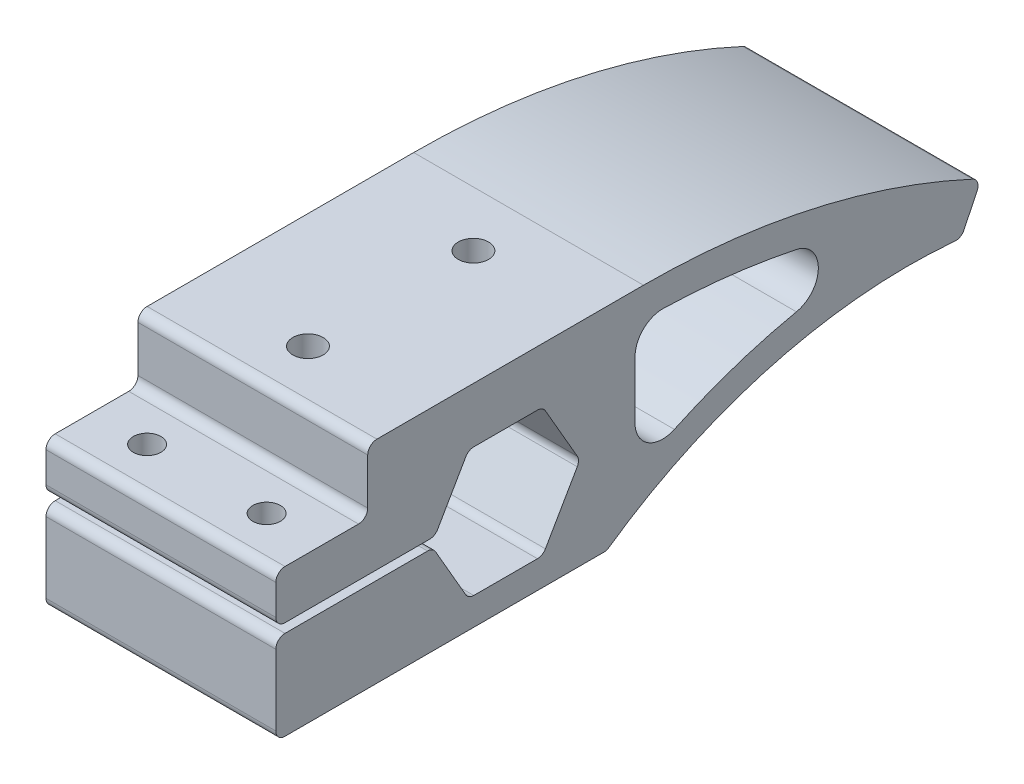
SolidWorks part; units mm, degrees
material "2014 Alloy"
ref_plane "Front Plane" through (0, 0, 0) normal (0, 0, 1) x (1, 0, 0)
ref_plane "Top Plane" through (0, 0, 0) normal (0, 1, 0) x (1, 0, 0)
ref_plane "Right Plane" through (0, 0, 0) normal (1, 0, 0) x (0, 0, -1)
sketch "Sketch1" plane through (0, 0, 0) normal (1, 0, 0) x (0, 0, -1)
  line L0 (0, 85) -> (-30, 85)
  line L1 (-30, 85) -> (-30, 78)
  line L2 (-30, 78) -> (-40, 78)
  line L3 (-40, 71.7) -> (-22.9097, 71.7)
  line L4 (-22.6788, 72.7) -> (-40, 72.7)
  line L5 (36.7289, 76.655) -> (34.5684, 72.1459)
  line L6 (-6.9171, 72) -> (-10.9585, 79)
  line L7 (-10.9585, 79) -> (-19.0415, 79)
  line L8 (-19.0415, 79) -> (-22.6788, 72.7)
  line L9 (-22.9097, 71.7) -> (-19.0415, 65)
  line L10 (-19.0415, 65) -> (-10.9585, 65)
  line L11 (-10.9585, 65) -> (-6.9171, 72)
  line L12 (-40, 72.7) -> (-40, 78)
  line L13 (-40, 71.7) -> (-40, 62)
  line L14 (-40, 62) -> (-4, 62)
  line L15 (-12.1097, 52.9939) -> (-16.8969, 61.2856) [skipped]
  line L17 (-0.9171, 72.4558) -> (-0.9171, 78.7311)
  circle A0 centre (0, 0) radius 85 construction
  arc A1 (0, 85) -> (36.7289, 76.655) centre (0, 0) cw
  circle A2 centre (-15, 72) radius 7 construction
  arc A3 (34.5684, 72.1459) -> (-4, 62) centre (28.8691, 15.4315) ccw
  arc A4 (-0.9171, 78.7311) -> (2.1631, 81.7301) centre (2.0829, 78.7311) cw
  arc A5 (-0.9171, 72.4558) -> (3.357, 69.7398) centre (2.0829, 72.4558) ccw
  arc A6 (2.1631, 81.7301) -> (16.6347, 80.0466) centre (-0.0247, -0.1191) cw
  arc A7 (3.357, 69.7398) -> (16.637, 74.1725) centre (28.938, 15.2109) cw
  arc A8 (16.6347, 80.0466) -> (16.637, 74.1725) centre (16.0243, 77.1093) cw
  dimension "D1" = 170
  dimension "D4" = 10
  dimension "D5" = 5
  dimension "D7" = 3
  dimension "D11" = 3
  dimension "D14" = 6
  dimension "D13" = 3
  dimension "D15" = 14
  dimension "D16" = 1
  dimension "D17" = 16
  dimension "D8" = 3
  dimension "D18" = 57
  dimension "D2" = 30
  dimension "D3" = 7
  dimension "D9" = 15
  dimension "D10" = 9.7
  dimension "D12" = 36
extrude "Boss-Extrude1" add sketch "Sketch1" along normal blind 25
fillet "Fillet1" radius 1 16 edges at (12.5, 85, 30) (12.5, 78, 30) (12.5, 78, 40) (12.5, 62, 40) (12.5, 76.655, -36.7289) (12.5, 65, 19.0415) (12.5, 71.7, 22.9097) (12.5, 72.7, 22.6788) (12.5, 79, 19.0415) (12.5, 79, 10.9585) (12.5, 72, 6.9171) (12.5, 65, 10.9585) (12.5, 72.7, 40) (12.5, 71.7, 40) (12.5, 62, 4) (12.5, 72.1459, -34.5684)
hole_wizard "Ø3.0mm Dowel Hole1" positions "Sketch3" profile "Sketch4" hole size "Ø3.0" standard "ISO" end condition through all
sketch "Sketch3" plane through (0, 78, 0) normal (0, 1, 0) x (1, 0, 0)
  line L0 (0, -31) -> (0, -39) construction
  line L1 (25, -31) -> (25, -39) construction
  line L2 (25, -40) -> (0, -40) construction
  point P0 (6, -35)
  point P2 (19, -35)
  dimension "D1" = 6
  dimension "D2" = 6
  dimension "D3" = 5
sketch "Sketch4" plane through (6, 78, 35) normal (1, 0, 0) x (0, 0, 1)
  line L0 (0, 0) -> (0, 16)
  line L1 (0, 16) -> (1.5, 16)
  line L2 (1.5, 16) -> (1.5, 0)
  line L5 (1.5, 0) -> (0, 0)
  line L11 (0, -6.35) -> (0, 107.95) construction
  dimension "Thru Hole Dia." = 3
  dimension "Thru Hole Depth" = 16
hole_wizard "M4 Tapped Hole1" positions "Sketch6" profile "Sketch7" tap size "M4" standard "ISO"
sketch "Sketch6" plane through (0, 85, 0) normal (0, 1, 0) x (1, 0, 0)
  line L0 (0, 0) -> (0, -29) construction
  line L1 (25, -30) -> (0, -30) construction
  point P10 (12.5, -24)
  point P17 (12.5, -6)
  dimension "D1" = 12.5
  dimension "D2" = 6
  dimension "D3" = 18
sketch "Sketch7" plane through (12.5, 85, 24) normal (1, 0, 0) x (0, 0, 1)
  line L0 (0, 0) -> (0, 11.0914)
  line L1 (0, 11.0914) -> (1.65, 10.1)
  line L2 (1.65, 10.1) -> (1.65, 0)
  line L5 (1.65, 0) -> (0, 0)
  line L10 (0, 11.0914) -> (-1.65, 10.1) construction
  line L11 (0, -6.35) -> (0, 107.95) construction
  dimension "Tap Drill Dia." = 3.3
  dimension "Tap Drill Depth" = 10.1
  dimension "Drill Angle" = 118
cosmetic thread "Hole Thread1" parameters "D1"=8, "D2"=4
cosmetic thread "Hole Thread3" parameters "D1"=8, "D2"=4
